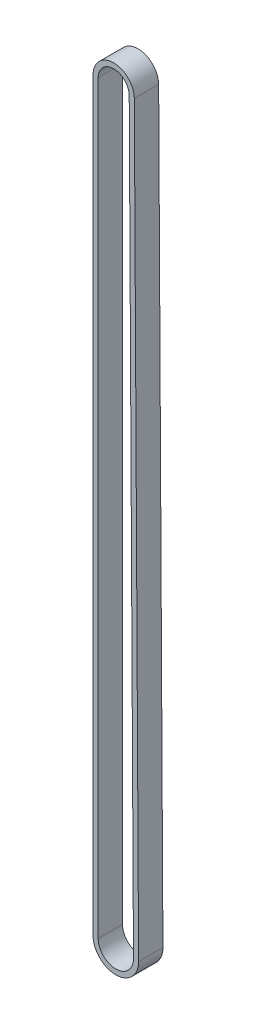
SolidWorks part; units mm, degrees
material "VITON"
ref_plane "Front Plane" through (0, 0, 0) normal (0, 0, 1) x (1, 0, 0)
ref_plane "Top Plane" through (0, 0, 0) normal (0, 1, 0) x (1, 0, 0)
ref_plane "Right Plane" through (0, 0, 0) normal (1, 0, 0) x (0, 0, -1)
sketch "Sketch1" plane through (0, 0, 0) normal (0, 0, 1) x (1, 0, 0)
  line L2 (324.7565, -302.4459) -> (324.7565, -112.5526)
  line L3 (336.3564, -302.4126) -> (335.2656, -112.5224)
  line L4 (326.0565, -302.4459) -> (326.0565, -112.5526)
  line L6 (335.0564, -302.4201) -> (333.9656, -112.5299)
  arc A0 (336.3564, -302.4126) -> (324.7565, -302.4459) centre (330.5565, -302.4459) cw
  arc A1 (335.2656, -112.5224) -> (324.7565, -112.5526) centre (330.0111, -112.5526) ccw
  circle A3 centre (330.5565, -302.4459) radius 9.4996 construction
  arc A7 (333.9656, -112.5299) -> (326.0565, -112.5526) centre (330.0111, -112.5526) ccw
  arc A9 (335.0564, -302.4201) -> (326.0565, -302.4459) centre (330.5565, -302.4459) cw
  circle A11 centre (330.5565, -302.4459) radius 6.2 construction
  point P7 (34.3966, -33.749)
  point P28 (35.5953, -32.4056)
  dimension "D1" = 18.9992
  dimension "D3" = 4.5
  dimension "D6" = 1.3
  dimension "D2" = 1.3
extrude "Boss-Extrude1" add sketch "Sketch1" against normal blind 6.2
